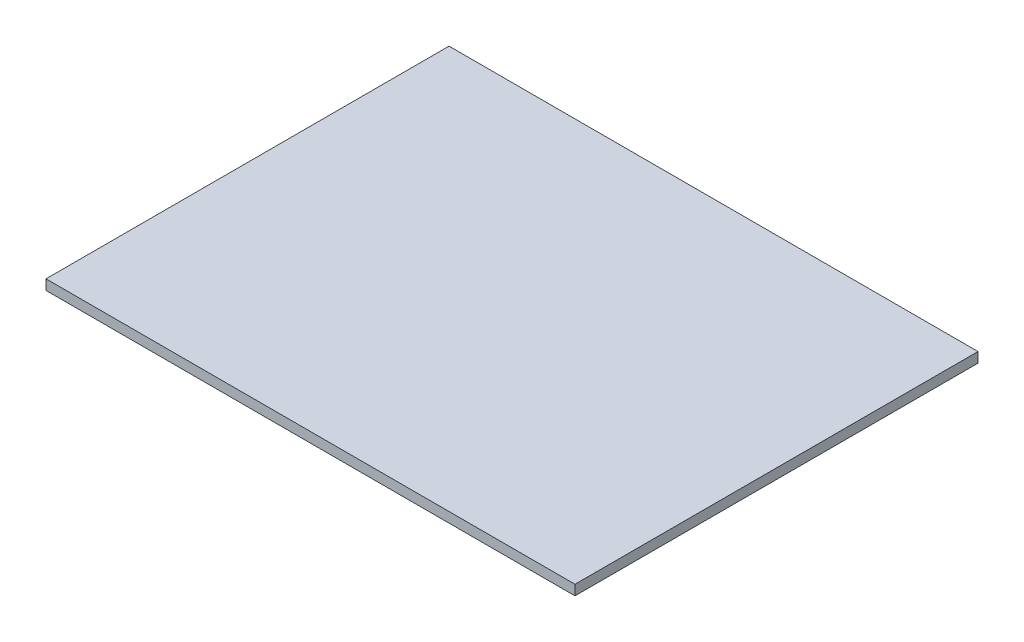
SolidWorks part; units mm, degrees
ref_plane "Front Plane" through (0, 0, 0) normal (0, 0, 1) x (1, 0, 0)
ref_plane "Top Plane" through (0, 0, 0) normal (0, 1, 0) x (1, 0, 0)
ref_plane "Right Plane" through (0, 0, 0) normal (1, 0, 0) x (0, 0, -1)
sketch "Sketch1" plane through (0, 0, 0) normal (0, 1, 0) x (1, 0, 0)
  line L1 (-105, -80) -> (105, -80)
  line L2 (-105, -80) -> (-105, 80)
  line L3 (-105, 80) -> (105, 80)
  line L4 (105, -80) -> (105, 80)
  line L5 (-105, -80) -> (105, 80) construction
  line L6 (-105, 80) -> (105, -80) construction
  point P0 (0, 0)
  dimension "D1" = 210
  dimension "D2" = 160
extrude "Boss-Extrude1" add sketch "Sketch1" along normal blind 4
